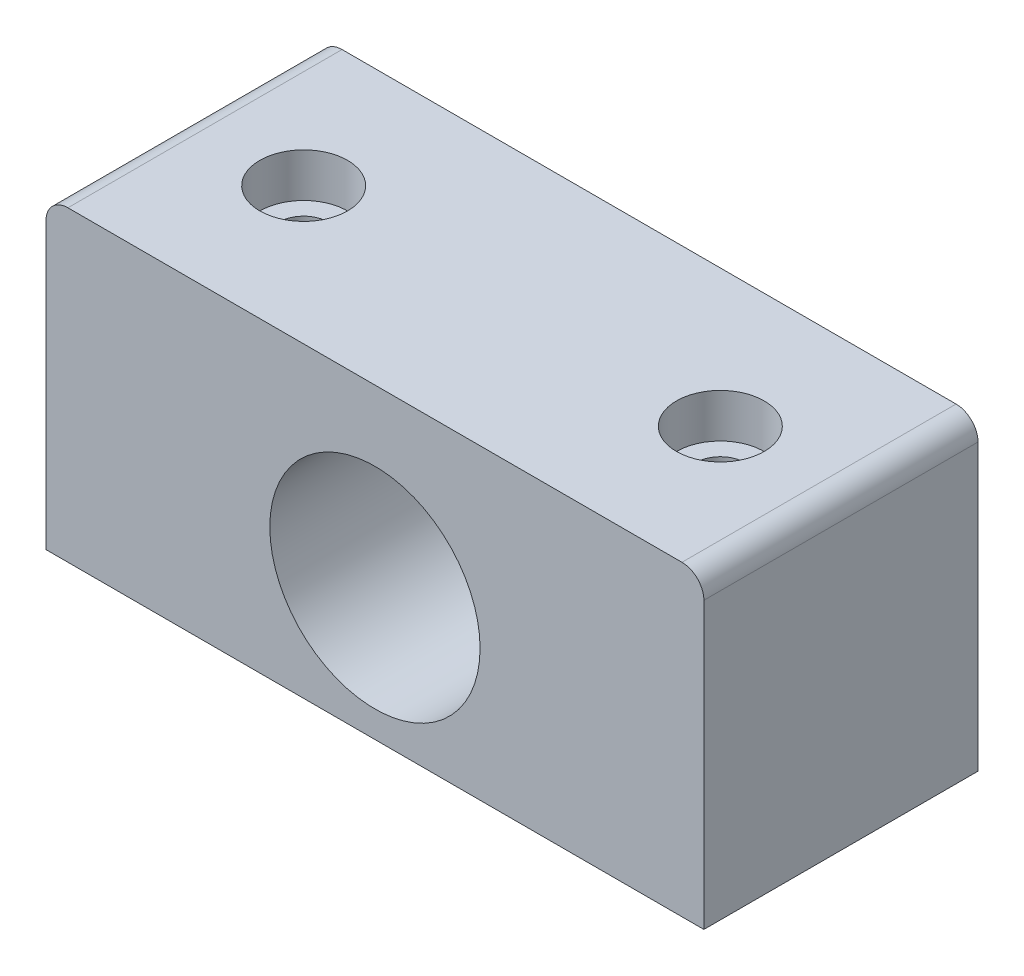
SolidWorks part; units mm, degrees
ref_plane "Front Plane" through (0, 0, 0) normal (0, 0, 1) x (1, 0, 0)
ref_plane "Top Plane" through (0, 0, 0) normal (0, 1, 0) x (1, 0, 0)
ref_plane "Right Plane" through (0, 0, 0) normal (1, 0, 0) x (0, 0, -1)
sketch "Sketch1" plane through (0, 0, 0) normal (0, 1, 0) x (1, 0, 0)
  line L1 (-30, -12.5) -> (30, -12.5)
  line L2 (-30, -12.5) -> (-30, 12.5)
  line L3 (-30, 12.5) -> (30, 12.5)
  line L4 (30, -12.5) -> (30, 12.5)
  line L5 (-30, -12.5) -> (30, 12.5) construction
  line L6 (-30, 12.5) -> (30, -12.5) construction
  point P0 (0, 0)
  dimension "D1" = 25
  dimension "D2" = 60
extrude "Boss-Extrude1" add sketch "Sketch1" along normal blind 28
sketch "Sketch2" plane through (0, 0, 12.5) normal (0, 0, 1) x (1, 0, 0)
  line L1 (-30, 0) -> (30, 0) construction
  circle A0 centre (0, 12) radius 9.5885
  point P2 (0, 0)
  dimension "D1" = 19.177
  dimension "D2" = 12
extrude "Cut-Extrude1" cut sketch "Sketch2" against normal through all contours A0
sketch "Sketch4" plane through (0, 28, 0) normal (0, 1, 0) x (1, 0, 0)
  line L0 (0, 12.5) -> (0, -12.5) construction
  line L1 (30, 12.5) -> (-30, 12.5) construction
  line L2 (-30, -12.5) -> (30, -12.5) construction
  line L3 (-30, 0) -> (30, 0) construction
  line L4 (-30, 12.5) -> (-30, -12.5) construction
  line L5 (30, -12.5) -> (30, 12.5) construction
  point P0 (-19, 0)
  point P1 (19, 0)
  point P8 (0, 0)
  dimension "D1" = 38
hole_wizard "CBORE for M4 SHCS1" positions "Sketch5" profile "Sketch6" counterbore size "M4" standard "ANSI Metric" end condition through all
sketch "Sketch5" plane through (0, 28, 0) normal (0, 1, 0) x (1, 0, 0)
  point P0 (-19, 0)
  point P3 (19, 0)
sketch "Sketch6" plane through (-19, 28, 0) normal (1, 0, 0) x (0, 0, 1)
  line L0 (0, 0) -> (0, 28)
  line L1 (0, 28) -> (2.25, 28)
  line L3 (2.25, 28) -> (2.25, 4)
  line L4 (2.25, 4) -> (4, 4)
  line L5 (4, 4) -> (4, 0)
  line L7 (4, 0) -> (0, 0)
  line L11 (0, -6.35) -> (0, 107.95) construction
  dimension "Thru Hole Dia." = 4.5
  dimension "Thru Hole Depth" = 28
  dimension "C'Bore Dia." = 8
  dimension "C'Bore Depth" = 4
fillet "Fillet1" radius 2 2 edges at (30, 28, 0) (-30, 28, 0)
